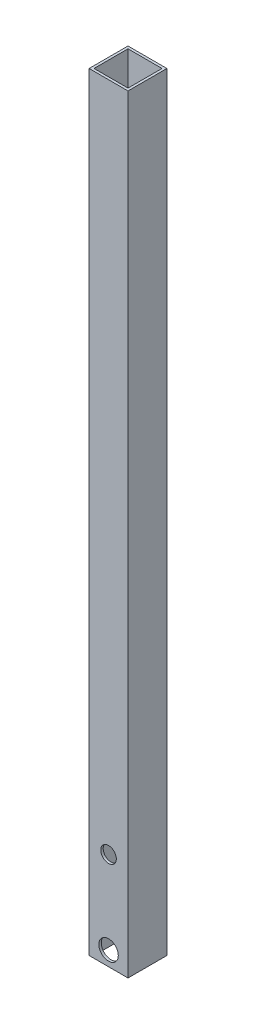
SolidWorks part; units mm, degrees
material "1060 Alloy"
ref_plane "Front Plane" through (0, 0, 0) normal (0, 0, 1) x (1, 0, 0)
ref_plane "Top Plane" through (0, 0, 0) normal (0, 1, 0) x (1, 0, 0)
ref_plane "Right Plane" through (0, 0, 0) normal (1, 0, 0) x (0, 0, -1)
sketch "Sketch1" plane through (0, 0, 0) normal (0, 1, 0) x (1, 0, 0)
  line L0 (-11.1125, 11.1125) -> (-11.1125, -11.1125)
  line L1 (-12.7, 12.7) -> (12.7, 12.7)
  line L2 (-12.7, 12.7) -> (-12.7, -12.7)
  line L3 (-12.7, -12.7) -> (12.7, -12.7)
  line L4 (12.7, 12.7) -> (12.7, -12.7)
  line L5 (-12.7, 12.7) -> (12.7, -12.7) construction
  line L6 (-12.7, -12.7) -> (12.7, 12.7) construction
  line L7 (-11.1125, -11.1125) -> (11.1125, -11.1125)
  line L8 (11.1125, 11.1125) -> (11.1125, -11.1125)
  line L9 (-11.1125, 11.1125) -> (11.1125, 11.1125)
  point P0 (0, 0)
  dimension "D1" = 25.4
  dimension "D2" = 25.4
  dimension "D3" = 1.5875
extrude "Boss-Extrude1" add sketch "Sketch1" along normal blind 501.65
sketch "Sketch4" plane through (0, 0, 12.7) normal (0, 0, 1) x (1, 0, 0)
  line L0 (0, 0) -> (0, 9.525) construction
  line L1 (-12.7, 0) -> (12.7, 0) construction
  circle A0 centre (0, 9.525) radius 6.35
  dimension "D1" = 12.7
  dimension "D2" = 9.525
extrude "Cut-Extrude1" cut sketch "Sketch4" against normal through all
sketch "Sketch7" plane through (0, 0, 12.7) normal (0, 0, 1) x (1, 0, 0)
  line L0 (-12.7, 501.65) -> (-12.7, 0) construction
  line L1 (-12.7, 0) -> (12.7, 0) construction
  circle A1 centre (0, 63.5) radius 5.08
  dimension "D3" = 10.16
  dimension "D1" = 12.7
  dimension "D2" = 63.5
extrude "Cut-Extrude3" cut sketch "Sketch7" against normal up to surface (1.5875 mm away) up to face at (-6.35, 9.525, 11.1125)
